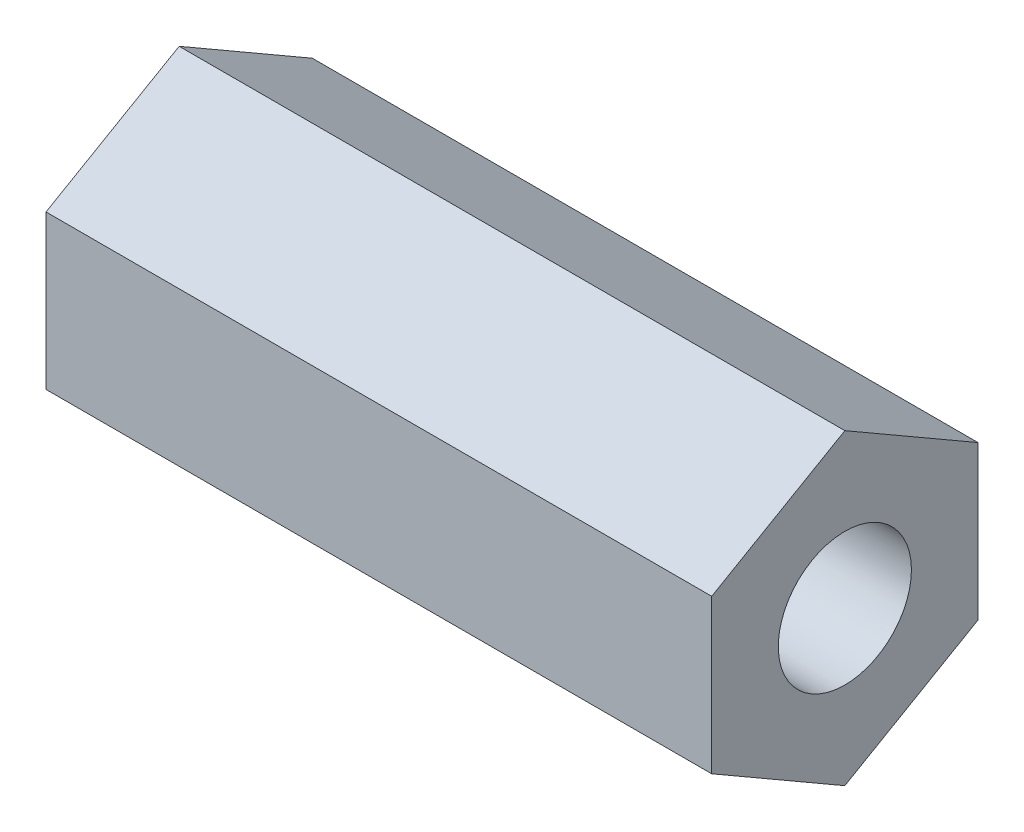
SolidWorks part; units mm, degrees
ref_plane "Front" through (0, 0, 0) normal (0, 0, 1) x (1, 0, 0)
ref_plane "Top" through (0, 0, 0) normal (0, 1, 0) x (1, 0, 0)
ref_plane "Right" through (0, 0, 0) normal (1, 0, 0) x (0, 0, -1)
sketch "草图1" plane through (0, 0, 0) normal (1, 0, 0) x (0, 0, -1)
  line L1 (-3, 1.7321) -> (-3, -1.7321)
  line L2 (-3, -1.7321) -> (0, -3.4641)
  line L3 (0, -3.4641) -> (3, -1.7321)
  line L4 (3, -1.7321) -> (3, 1.7321)
  line L5 (3, 1.7321) -> (0, 3.4641)
  line L6 (0, 3.4641) -> (-3, 1.7321)
  circle A0 centre (0, 0) radius 1.5
  circle A1 centre (0, 0) radius 3 construction
  dimension "D1" = 3
  dimension "D2" = 6
extrude "凸台-拉伸1" add sketch "草图1" along normal blind 15
